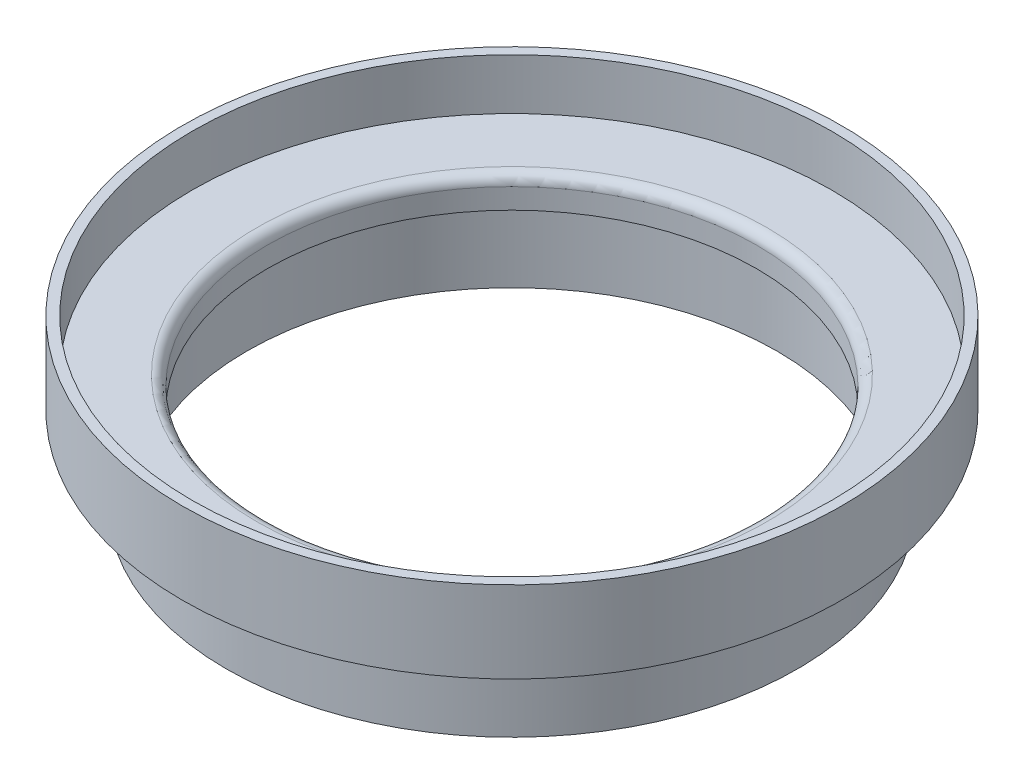
SolidWorks part; units mm, degrees
material "6061-T6 (SS)"
ref_plane "Front Plane" through (0, 0, 0) normal (0, 0, 1) x (1, 0, 0)
ref_plane "Top Plane" through (0, 0, 0) normal (0, 1, 0) x (1, 0, 0)
ref_plane "Right Plane" through (0, 0, 0) normal (1, 0, 0) x (0, 0, -1)
ref_axis "Axis1" through (0, 55, 0) along (0, -1, 0)
sketch "Cross Section" plane through (0, 0, 0) normal (0, 0, 1) x (1, 0, 0)
  line L0 (-38.1, 0) -> (-38.1, -3.175)
  line L1 (-38.1, -3.175) -> (-41.275, -3.175)
  line L2 (-41.275, -3.175) -> (-41.275, -15.875)
  line L4 (0, -15.875) -> (-38.1, -15.875) construction
  line L5 (-44.45, -15.875) -> (-44.45, -3.175)
  line L6 (-44.45, -3.175) -> (-51.308, -3.175)
  line L7 (-51.308, -3.175) -> (-51.308, 9.525)
  line L8 (-51.308, 9.525) -> (-49.784, 9.525)
  line L9 (-49.784, 9.525) -> (-49.784, 1.5875)
  line L11 (-38.1, 0) -> (0, 0) construction
  line L13 (-44.45, -15.875) -> (-41.275, -15.875)
  line L14 (-49.784, 1.5875) -> (-49.784, 3.175) construction
  line L15 (-39.6875, 1.5875) -> (-49.784, 1.5875)
  arc A0 (-39.6875, 1.5875) -> (-38.1, 0) centre (-39.6875, 0) cw
  dimension "D2" = 1.5875
  dimension "D1" = 3.175
  dimension "D3" = 3.175
  dimension "D4" = 1.5875
  dimension "D5" = 6.858
  dimension "D6" = 12.7
  dimension "D7" = 38.1
  dimension "D9" = 3.175
revolve "Main" add sketch "Cross Section" angle 360 about axis through (0, 55, 0) along (0, -1, 0)
